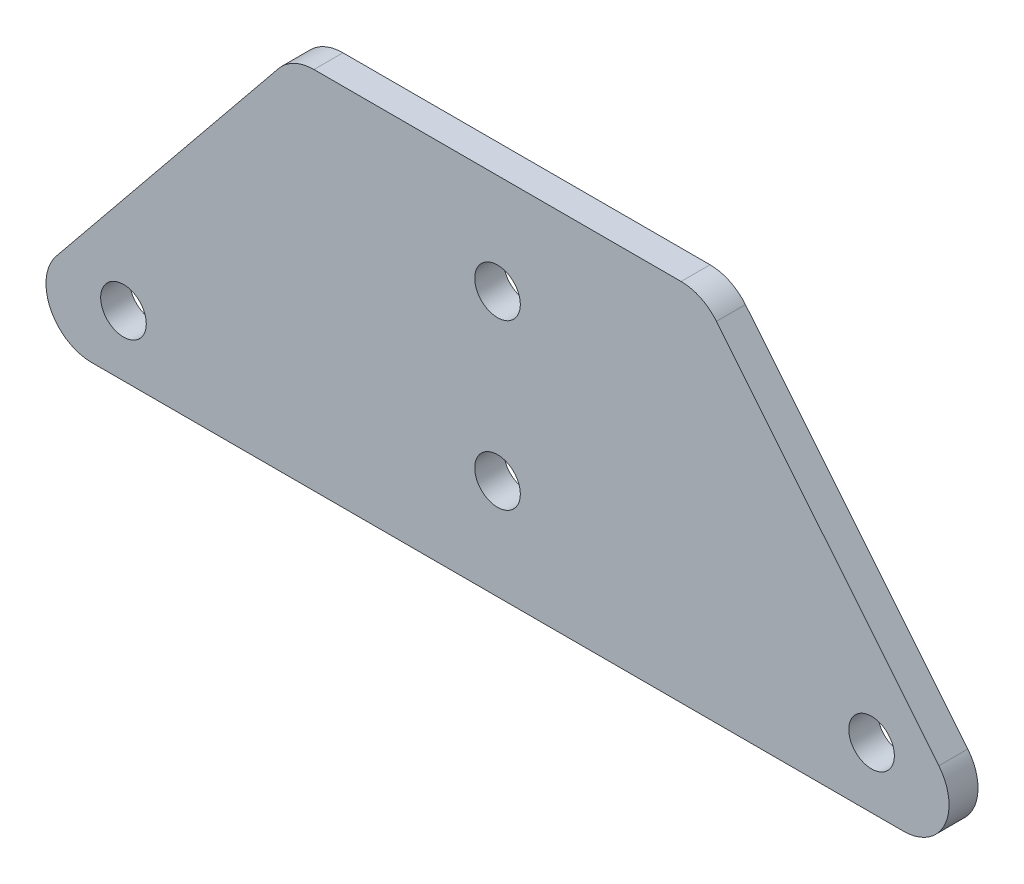
SolidWorks part; units mm, degrees
material "1060 Alloy"
ref_plane "Front Plane" through (0, 0, 0) normal (0, 0, 1) x (1, 0, 0)
ref_plane "Top Plane" through (0, 0, 0) normal (0, 1, 0) x (1, 0, 0)
ref_plane "Right Plane" through (0, 0, 0) normal (1, 0, 0) x (0, 0, -1)
sketch "Sketch1" plane through (0, 0, 0) normal (0, 0, 1) x (1, 0, 0)
  line L0 (-44.4951, -23.153) -> (44.4951, -23.153)
  line L1 (48.3757, -15) -> (24.0007, 15)
  line L2 (20.1201, 16.847) -> (-20.1201, 16.847)
  line L3 (-24.0007, 15) -> (-48.3757, -15)
  line L4 (0, 5.847) -> (0, 16.847) construction
  line L5 (0, -12.153) -> (0, -23.153) construction
  line L6 (-41, -16.4894) -> (0, -16.4894) construction
  line L7 (0, -16.4894) -> (41, -16.4894) construction
  line L8 (-48.3757, -15) -> (-41, -16.4894) construction
  line L9 (-41, -16.4894) -> (-44.4951, -23.153) construction
  arc A0 (44.4951, -23.153) -> (48.3757, -15) centre (44.4951, -18.153) ccw
  arc A1 (-44.4951, -23.153) -> (-48.3757, -15) centre (-44.4951, -18.153) cw
  arc A2 (24.0007, 15) -> (20.1201, 16.847) centre (20.1201, 11.847) ccw
  arc A3 (-20.1201, 16.847) -> (-24.0007, 15) centre (-20.1201, 11.847) ccw
  circle A4 centre (0, 5.847) radius 2.5
  circle A5 centre (0, -12.153) radius 2.5
  circle A6 centre (-41, -16.4894) radius 2.5
  circle A7 centre (41, -16.4894) radius 2.5
  point P2 (0, 16.847)
  point P5 (-36.1882, 0)
  point P11 (55, -23.153)
  point P14 (-55, -23.153)
  point P17 (22.5, 16.847)
  point P20 (-22.5, 16.847)
  dimension "D4" = 5
  dimension "D5" = 18
  dimension "D6" = 5
  dimension "D7" = 82
  dimension "D1" = 45
  dimension "D2" = 110
  dimension "D3" = 40
extrude "Boss-Extrude1" add sketch "Sketch1" along normal blind 3.175
